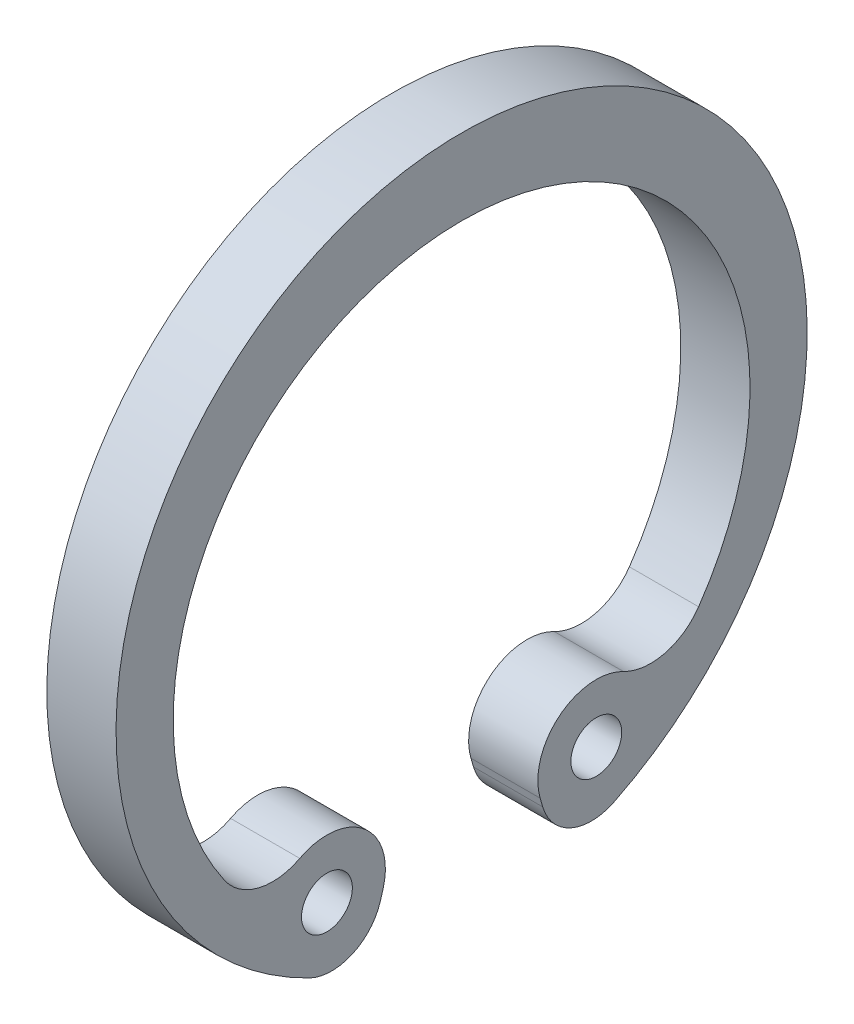
SolidWorks part; units mm, degrees
ref_plane "Front Plane" through (0, 0, 0) normal (0, 0, 1) x (1, 0, 0)
ref_plane "Top Plane" through (0, 0, 0) normal (0, 1, 0) x (1, 0, 0)
ref_plane "Right Plane" through (0, 0, 0) normal (1, 0, 0) x (0, 0, -1)
ref_plane "Plane1" through (0.6, 0, 0) normal (1, 0, 0) x (0, 0, -1)
sketch "Sketch1" plane through (0.6, 0, 0) normal (1, 0, 0) x (0, 0, -1)
  line L0 (-1.4066, -4.8331) -> (-1.362, -4.6796)
  line L1 (1.362, -4.6796) -> (1.4066, -4.8331)
  circle A0 centre (-2.3348, -4.3965) radius 0.4405
  circle A1 centre (2.3348, -4.3965) radius 0.4405
  arc A2 (1.4066, -4.8331) -> (2.6409, -5.3777) centre (2.2526, -4.5869) ccw
  arc A3 (2.6409, -5.3777) -> (-2.6409, -5.3777) centre (0, 0) ccw
  arc A4 (-2.6409, -5.3777) -> (-1.4066, -4.8331) centre (-2.2526, -4.5869) ccw
  arc A5 (-1.362, -4.6796) -> (-2.8056, -3.4992) centre (-2.3348, -4.3965) ccw
  arc A6 (-2.8056, -3.4992) -> (-4.1089, -3.1793) centre (-3.2763, -2.602) cw
  arc A7 (-4.1089, -3.1793) -> (4.1089, -3.1793) centre (0, -0.3304) cw
  arc A8 (4.1089, -3.1793) -> (2.8056, -3.4992) centre (3.2763, -2.602) cw
  arc A9 (2.8056, -3.4992) -> (1.362, -4.6796) centre (2.3348, -4.3965) ccw
  dimension "D1" = 5
extrude "Boss-Extrude1" add sketch "Sketch1" against normal blind 1.2
